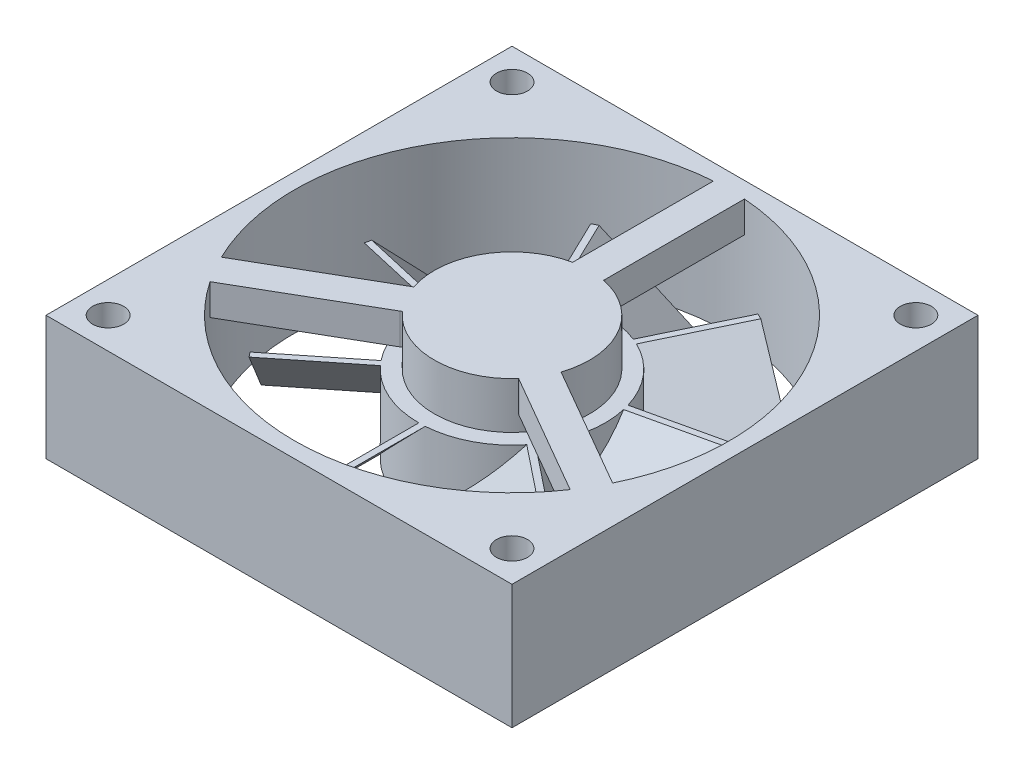
SolidWorks part; units mm, degrees
material "delrin"
ref_plane "Front Plane" through (0, 0, 0) normal (0, 0, 1) x (1, 0, 0)
ref_plane "Top Plane" through (0, 0, 0) normal (0, 1, 0) x (1, 0, 0)
ref_plane "Right Plane" through (0, 0, 0) normal (1, 0, 0) x (0, 0, -1)
sketch "Sketch1" plane through (0, 0, 0) normal (0, 1, 0) x (1, 0, 0)
  line L1 (-15, 15) -> (15, 15)
  line L2 (-15, 15) -> (-15, -15)
  line L3 (-15, -15) -> (15, -15)
  line L4 (15, 15) -> (15, -15)
  line L5 (-15, 15) -> (15, -15) construction
  line L6 (-15, -15) -> (15, 15) construction
  circle A0 centre (0, 0) radius 14
  point P0 (0, 0)
  dimension "D2" = 28
  dimension "D1" = 30
extrude "Boss-Extrude1" add sketch "Sketch1" along normal blind 8
sketch "Sketch2" plane through (0, 0, 0) normal (0, 1, 0) x (1, 0, 0)
  circle A0 centre (0, 0) radius 5
  dimension "D1" = 10
extrude "Boss-Extrude2" add sketch "Sketch2" along normal blind 8 separate body
sketch "Sketch3" plane through (0, 8, 0) normal (0, 1, 0) x (1, 0, 0)
  line L0 (0, 5) -> (0, 0) construction
  line L1 (0, 0) -> (-4.3301, -2.5) construction
  line L2 (0, 0) -> (4.3301, -2.5) construction
  line L3 (0, 5) -> (0, 14) construction
  line L4 (-1, 5) -> (-1, 14)
  line L5 (1, 5) -> (1, 14)
  line L6 (-4.3301, -2.5) -> (-12.1244, -7) construction
  line L7 (-3.8301, -3.366) -> (-11.6244, -7.866)
  line L8 (-4.8301, -1.634) -> (-12.6244, -6.134)
  line L9 (4.3301, -2.5) -> (12.1244, -7) construction
  line L10 (4.8301, -1.634) -> (12.6244, -6.134)
  line L11 (3.8301, -3.366) -> (11.6244, -7.866)
  circle A0 centre (0, 0) radius 5 construction
  circle A1 centre (0, 0) radius 14 construction
  arc A2 (-1, 5) -> (1, 5) centre (0, 5) ccw
  arc A3 (1, 14) -> (-1, 14) centre (0, 14) ccw
  arc A4 (-3.8301, -3.366) -> (-4.8301, -1.634) centre (-4.3301, -2.5) ccw
  arc A5 (-12.6244, -6.134) -> (-11.6244, -7.866) centre (-12.1244, -7) ccw
  arc A6 (4.8301, -1.634) -> (3.8301, -3.366) centre (4.3301, -2.5) ccw
  arc A7 (11.6244, -7.866) -> (12.6244, -6.134) centre (12.1244, -7) ccw
  point P5 (0, 9.5)
  point P16 (-8.2272, -4.75)
  point P22 (8.2272, -4.75)
  dimension "D3" = 1
  dimension "D4" = 1
  dimension "D5" = 1
  dimension "D1" = 120
  dimension "D2" = 120
extrude "Boss-Extrude3" add sketch "Sketch3" against normal blind 2
sketch "Sketch4" plane through (0, 8, 0) normal (0, 1, 0) x (1, 0, 0)
  line L0 (15, 15) -> (-15, 15) construction
  line L1 (-15, 15) -> (-15, -15) construction
  line L2 (15, -15) -> (15, 15) construction
  line L3 (-15, -15) -> (15, -15) construction
  circle A0 centre (-13, 13) radius 1
  circle A1 centre (13, 13) radius 1
  circle A2 centre (13, -13) radius 1
  circle A3 centre (-13, -13) radius 1
  dimension "D1" = 2
  dimension "D2" = 2
  dimension "D4" = 2
  dimension "D5" = 2
  dimension "D6" = 2
  dimension "D7" = 2
  dimension "D8" = 2
  dimension "D9" = 2
  dimension "D3" = 2
hole_wizard "Ø2.0mm Dowel Hole1" positions "Sketch5" profile "Sketch6" hole size "Ø2.0" standard "ANSI Metric" end condition up to next
sketch "Sketch5" plane through (0, 8, 0) normal (0, 1, 0) x (1, 0, 0)
  point P0 (13, 13)
  point P3 (-13, 13)
  point P6 (-13, -13)
  point P9 (13, -13)
sketch "Sketch6" plane through (13, 8, -13) normal (1, 0, 0) x (0, 0, 1)
  line L0 (0, 0) -> (0, 8)
  line L1 (0, 8) -> (1, 8)
  line L2 (1, 8) -> (1, 0)
  line L5 (1, 0) -> (0, 0)
  line L11 (0, -6.35) -> (0, 107.95) construction
  dimension "Thru Hole Dia." = 2
  dimension "Thru Hole Depth" = 8
sketch "Sketch7" plane through (0, 0, 0) normal (0, -1, 0) x (1, 0, 0)
  circle A0 centre (0, 0) radius 6
  circle A1 centre (0, 0) radius 5 construction
  dimension "D1" = 1
extrude "Boss-Extrude4" add sketch "Sketch7" against normal blind 5
sketch "Sketch9" plane through (0, 0, 0) normal (0, 0, 1) x (1, 0, 0)
  line L0 (0, 5) -> (-4.899, 0)
  line L1 (6, 5) -> (-6, 5) construction
  line L2 (-6, 0) -> (6, 0) construction
  line L3 (-4.899, 0) -> (-4.499, 0)
  line L4 (-4.499, 0) -> (0.4, 5)
  line L5 (0.4, 5) -> (0, 5)
  dimension "D1" = 7
  dimension "D2" = 0.4
extrude "Boss-Extrude5" add sketch "Sketch9" along normal blind 12
sketch "Sketch10" plane through (0, 0, 0) normal (1, 0, 0) x (0, 0, -1)
  line L0 (0, 0) -> (0, 14.1462)
pattern_circular "CirPattern1" count 7 over 360 about axis through (0, 0, 0) along (0, 1, 0) of "Boss-Extrude5"
